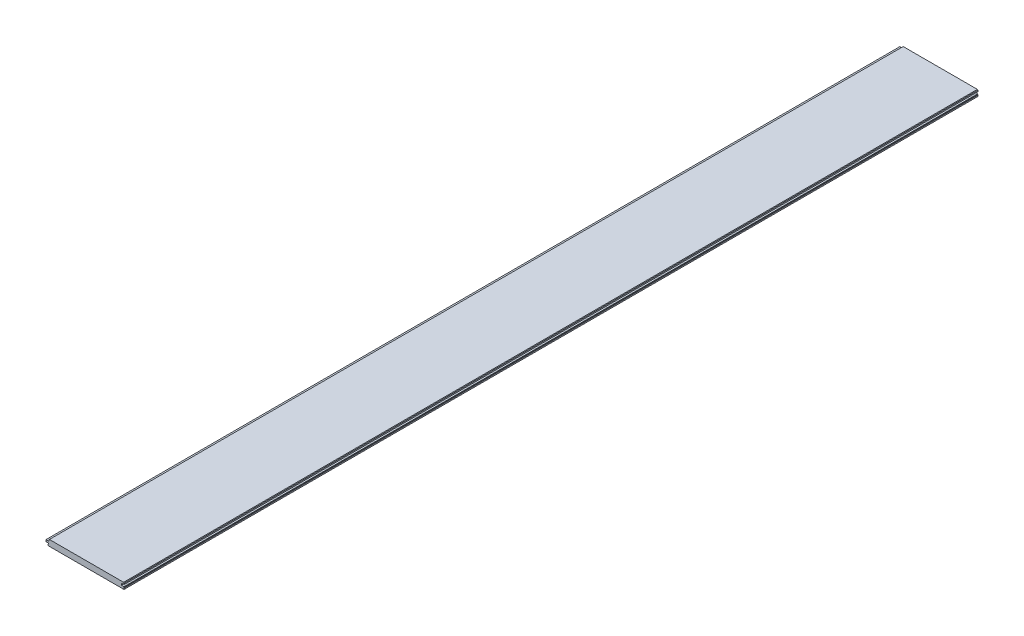
SolidWorks part; units mm, degrees
ref_plane "Front Plane" through (0, 0, 0) normal (0, 0, 1) x (1, 0, 0)
ref_plane "Top Plane" through (0, 0, 0) normal (0, 1, 0) x (1, 0, 0)
ref_plane "Right Plane" through (0, 0, 0) normal (1, 0, 0) x (0, 0, -1)
sketch "Sketch1" plane through (0, 0, 0) normal (0, 0, 1) x (1, 0, 0)
  line L0 (-93.1355, 2.9845) -> (-100.3745, 2.9845)
  line L1 (-95.1675, 7.5565) -> (95.1675, 7.5565)
  line L2 (-95.1675, 7.5565) -> (-95.1675, -7.5565)
  line L3 (-95.1675, -7.5565) -> (95.1675, -7.5565)
  line L4 (95.1675, 7.5565) -> (95.1675, -7.5565)
  line L5 (-95.1675, 7.5565) -> (95.1675, -7.5565) construction
  line L6 (-95.1675, -7.5565) -> (95.1675, 7.5565) construction
  line L7 (-100.3745, 2.9845) -> (-100.3745, -1.5875)
  line L8 (-100.3745, -1.5875) -> (-95.1675, -1.5875)
  line L9 (-95.1675, -1.5875) -> (-95.1675, -7.5565)
  line L10 (94.8372, 3.1242) -> (87.9158, 3.1242)
  line L11 (87.9158, 3.1242) -> (87.9158, -1.4986)
  line L12 (87.9158, -1.4986) -> (94.5324, -1.4986)
  line L13 (94.5324, -1.4986) -> (94.5324, -3.1115)
  line L14 (-93.1355, 2.9845) -> (-93.1355, 7.5565)
  line L15 (-93.1355, 6.2865) -> (-91.8654, 7.5565)
  line L16 (-95.1675, -1.5875) -> (-94.5324, -1.5875)
  line L17 (-94.5324, -1.5875) -> (-94.5324, -3.1115)
  line L18 (-94.5324, -3.1115) -> (-95.1675, -3.7465)
  line L19 (-94.5324, -7.5565) -> (-95.1675, -6.9215)
  line L20 (94.8372, 3.1242) -> (94.8372, 7.5565)
  line L21 (94.5324, -3.1115) -> (95.1675, -3.7465)
  line L22 (94.5324, -7.5565) -> (95.1675, -6.9215)
  line L23 (94.8372, 6.2865) -> (93.5672, 7.5565)
  dimension "D1" = 190.3349
  dimension "D2" = 15.113
  dimension "D3" = 9.144
  dimension "D4" = 7.239
  dimension "D5" = 4.572
  dimension "D6" = 5.207
  dimension "D7" = 6.0579
  dimension "D8" = 4.6228
  dimension "D9" = 0.635
  dimension "D10" = 6.9215
  dimension "D11" = 45
  dimension "D12" = 1.27
  dimension "D13" = 3.81
  dimension "D14" = 0.635
  dimension "D15" = 45
  dimension "D16" = 0.635
  dimension "D17" = 45
  dimension "D18" = 7.2517
  dimension "D19" = 1.27
extrude "Boss-Extrude1" add sketch "Sketch1" along normal mid plane 2133.6 contours L13 L12 L11 L10 L4 L1 L2 L8 L9 L3 | L7 L8 L2 L0
ref_plane "Plane1" through (0, 0, -1117.6) normal (0, 0, -1) x (-1, 0, 0)
sketch "Sketch2" plane through (0, 0, -1117.6) normal (0, 0, 1) x (1, 0, 0)
  line L0 (-94.5324, -7.5565) -> (94.5325, -7.5565) construction
  line L1 (-94.5324, -7.5565) -> (94.5325, -7.5565)
  point P2 (0, -7.5565)
